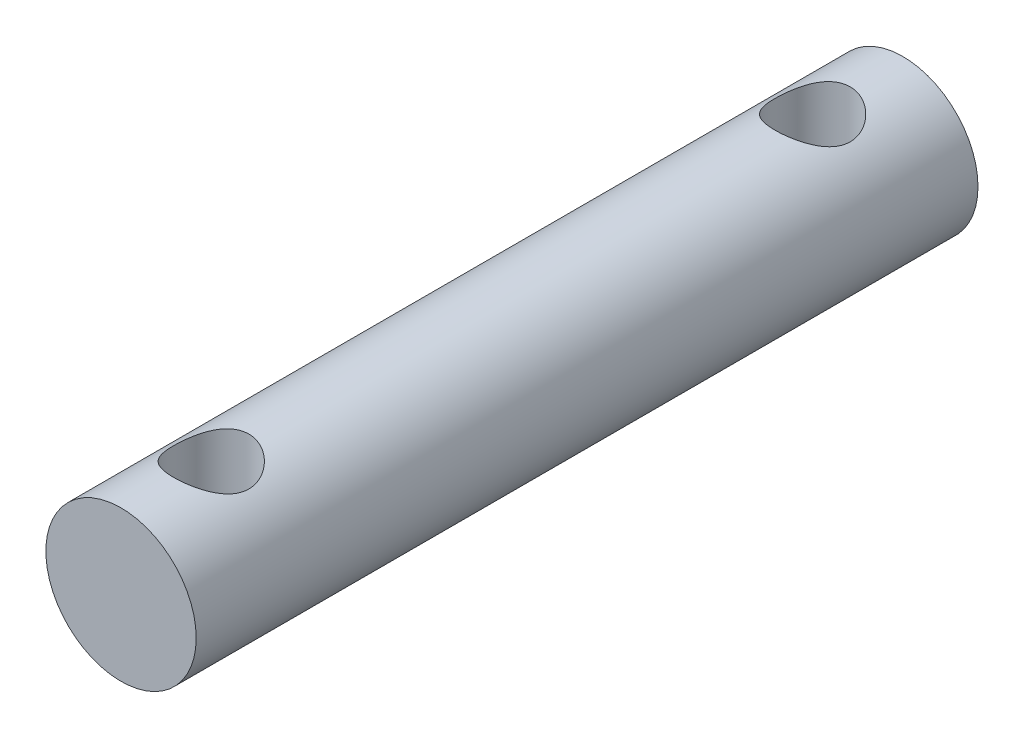
SolidWorks part; units mm, degrees
material "AISI 304"
ref_plane "Front Plane" through (0, 0, 0) normal (0, 0, 1) x (1, 0, 0)
ref_plane "Top Plane" through (0, 0, 0) normal (0, 1, 0) x (1, 0, 0)
ref_plane "Right Plane" through (0, 0, 0) normal (1, 0, 0) x (0, 0, -1)
sketch "Sketch1" plane through (0, 0, 0) normal (0, 0, 1) x (1, 0, 0)
  circle A0 centre (0.7723, 0) radius 2.5
extrude "Boss-Extrude1" add sketch "Sketch1" along normal blind 26
sketch "Sketch2" plane through (0, 0, 0) normal (0, 1, 0) x (1, 0, 0)
  line L0 (-1.7277, -26) -> (3.2723, -26) construction
  circle A0 centre (0.7723, -3) radius 1.25
  circle A1 centre (0.7723, -23) radius 1.25
  dimension "D1" = 20
  dimension "D2" = 3
extrude "Cut-Extrude1" cut sketch "Sketch2" against normal through all both and the other way through all
